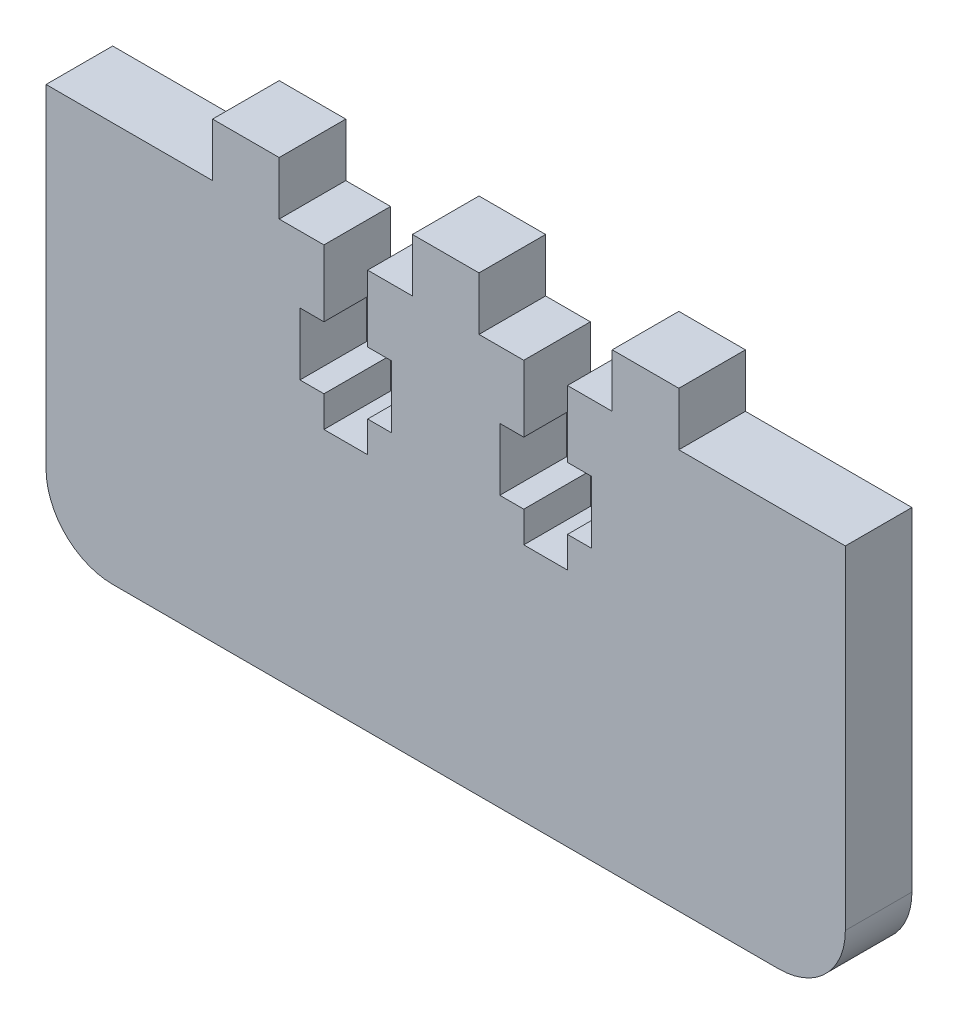
SolidWorks part; units mm, degrees
material "Acrylic (BLUE)"
ref_plane "Front Plane" through (0, 0, 0) normal (0, 0, 1) x (1, 0, 0)
ref_plane "Top Plane" through (0, 0, 0) normal (0, 1, 0) x (1, 0, 0)
ref_plane "Right Plane" through (0, 0, 0) normal (1, 0, 0) x (0, 0, -1)
sketch "Sketch1" plane through (0, 0, 0) normal (0, 0, 1) x (1, 0, 0)
  line L0 (-38.1, 19.05) -> (38.1, -19.05) construction
  line L1 (-38.1, 19.05) -> (38.1, 19.05)
  line L2 (-38.1, 19.05) -> (-38.1, -19.05)
  line L3 (-38.1, -19.05) -> (38.1, -19.05)
  line L4 (38.1, 19.05) -> (38.1, -19.05)
  dimension "D1" = 76.2
  dimension "D2" = 38.1
extrude "Boss-Extrude1" add sketch "Sketch1" along normal blind 6.35
sketch "Sketch2" plane through (0, 0, 6.35) normal (0, 0, 1) x (1, 0, 0)
  line L0 (0, 0) -> (0, 24.13) construction
  line L1 (38.1, 19.05) -> (-38.1, 19.05) construction
  line B0 (-11.6078, 19.05) -> (-11.6078, 12.7)
  line B1 (-11.6078, 12.7) -> (-13.8938, 12.7)
  line B2 (-13.8938, 12.7) -> (-13.8938, 6.7564)
  line B3 (-13.8938, 6.7564) -> (-11.6078, 6.7564)
  line B4 (-11.6078, 6.7564) -> (-11.6078, 3.81)
  line B5 (-11.6078, 3.81) -> (-7.4422, 3.81)
  line B6 (-7.4422, 3.81) -> (-7.4422, 6.7564)
  line B7 (-7.4422, 6.7564) -> (-5.1562, 6.7564)
  line B8 (-5.1562, 6.7564) -> (-5.1562, 12.7)
  line B9 (-5.1562, 12.7) -> (-7.4422, 12.7)
  line B10 (-7.4422, 12.7) -> (-7.4422, 19.05)
  line B11 (-7.4422, 19.05) -> (-3.175, 19.05)
  line B12 (-3.175, 19.05) -> (-3.175, 24.13)
  line B13 (-3.175, 24.13) -> (3.175, 24.13)
  line B14 (3.175, 24.13) -> (3.175, 19.05)
  line B15 (-11.6078, 19.05) -> (-15.875, 19.05)
  line B16 (-15.875, 19.05) -> (-15.875, 24.13)
  line B17 (-15.875, 24.13) -> (-22.225, 24.13)
  line B18 (-22.225, 24.13) -> (-22.225, 19.05)
  line B19 (-7.4422, 19.05) -> (-11.6078, 19.05) construction
  line B20 (22.225, 24.13) -> (22.225, 19.05)
  line B21 (7.4422, 19.05) -> (7.4422, 12.7)
  line B22 (7.4422, 12.7) -> (5.1562, 12.7)
  line B23 (5.1562, 12.7) -> (5.1562, 6.7564)
  line B24 (5.1562, 6.7564) -> (7.4422, 6.7564)
  line B25 (7.4422, 6.7564) -> (7.4422, 3.81)
  line B26 (7.4422, 3.81) -> (11.6078, 3.81)
  line B27 (11.6078, 3.81) -> (11.6078, 6.7564)
  line B28 (11.6078, 6.7564) -> (13.8938, 6.7564)
  line B29 (13.8938, 6.7564) -> (13.8938, 12.7)
  line B30 (13.8938, 12.7) -> (11.6078, 12.7)
  line B31 (11.6078, 12.7) -> (11.6078, 19.05)
  line B32 (15.875, 19.05) -> (15.875, 24.13)
  line B33 (15.875, 24.13) -> (22.225, 24.13)
  line B34 (7.4422, 19.05) -> (3.175, 19.05)
  line B35 (11.6078, 19.05) -> (7.4422, 19.05) construction
sketch_block_instance "NUT_HOLE_2X-1"
sketch_block "NUT_HOLE_2X" parameters "D1"=6.35, "D2"=4.1656, "D3"=25.4, "D4"=5.08, "D5"=8.7376, "D6"=5.9436, "D7"=6.35, "D8"=20.32, "D9"=2
sketch "Sketch3" plane through (0, 0, 6.35) normal (0, 0, 1) x (1, 0, 0)
  line L0 (22.225, 19.05) -> (15.875, 19.05)
  line L1 (-22.225, 24.13) -> (-22.225, 19.05) construction
  line L2 (-15.875, 24.13) -> (-22.225, 24.13) construction
  line L3 (-15.875, 19.05) -> (-15.875, 24.13) construction
  line L4 (-3.175, 24.13) -> (3.175, 24.13) construction
  line L5 (3.175, 24.13) -> (3.175, 19.05) construction
  line L6 (-3.175, 19.05) -> (-3.175, 24.13) construction
  line L7 (15.875, 24.13) -> (22.225, 24.13) construction
  line L8 (22.225, 24.13) -> (22.225, 19.05) construction
  line L9 (15.875, 19.05) -> (15.875, 24.13) construction
  line L10 (-22.225, 24.13) -> (-22.225, 19.05)
  line L11 (-15.875, 24.13) -> (-22.225, 24.13)
  line L12 (-15.875, 19.05) -> (-15.875, 24.13)
  line L13 (-3.175, 24.13) -> (3.175, 24.13)
  line L14 (3.175, 24.13) -> (3.175, 19.05)
  line L15 (-3.175, 19.05) -> (-3.175, 24.13)
  line L16 (15.875, 24.13) -> (22.225, 24.13)
  line L17 (22.225, 24.13) -> (22.225, 19.05)
  line L18 (15.875, 19.05) -> (15.875, 24.13)
  line L19 (-22.225, 19.05) -> (-15.875, 19.05)
  line L21 (-3.175, 19.05) -> (3.175, 19.05)
extrude "Boss-Extrude2" add sketch "Sketch3" against normal blind 6.35
sketch "Sketch6" plane through (0, 0, 6.35) normal (0, 0, 1) x (1, 0, 0)
  line L0 (-11.6078, 19.05) -> (-11.6078, 12.7) construction
  line L1 (-11.6078, 12.7) -> (-13.8938, 12.7) construction
  line L2 (-13.8938, 12.7) -> (-13.8938, 6.7564) construction
  line L3 (-13.8938, 6.7564) -> (-11.6078, 6.7564) construction
  line L4 (-11.6078, 6.7564) -> (-11.6078, 3.81) construction
  line L5 (-11.6078, 3.81) -> (-7.4422, 3.81) construction
  line L6 (-7.4422, 3.81) -> (-7.4422, 6.7564) construction
  line L7 (-7.4422, 6.7564) -> (-5.1562, 6.7564) construction
  line L8 (-5.1562, 6.7564) -> (-5.1562, 12.7) construction
  line L9 (-5.1562, 12.7) -> (-7.4422, 12.7) construction
  line L10 (-7.4422, 12.7) -> (-7.4422, 19.05) construction
  line L11 (7.4422, 19.05) -> (7.4422, 12.7) construction
  line L12 (7.4422, 12.7) -> (5.1562, 12.7) construction
  line L13 (5.1562, 12.7) -> (5.1562, 6.7564) construction
  line L14 (5.1562, 6.7564) -> (7.4422, 6.7564) construction
  line L15 (7.4422, 6.7564) -> (7.4422, 3.81) construction
  line L16 (11.6078, 3.81) -> (11.6078, 6.7564) construction
  line L17 (11.6078, 6.7564) -> (13.8938, 6.7564) construction
  line L18 (13.8938, 6.7564) -> (13.8938, 12.7) construction
  line L19 (13.8938, 12.7) -> (11.6078, 12.7) construction
  line L20 (11.6078, 12.7) -> (11.6078, 19.05) construction
  line L21 (7.4422, 3.81) -> (11.6078, 3.81) construction
  line L22 (-11.6078, 19.05) -> (-11.6078, 12.7)
  line L23 (-11.6078, 12.7) -> (-13.8938, 12.7)
  line L24 (-13.8938, 12.7) -> (-13.8938, 6.7564)
  line L25 (-13.8938, 6.7564) -> (-11.6078, 6.7564)
  line L26 (-11.6078, 6.7564) -> (-11.6078, 3.81)
  line L27 (-11.6078, 3.81) -> (-7.4422, 3.81)
  line L28 (-7.4422, 3.81) -> (-7.4422, 6.7564)
  line L29 (-7.4422, 6.7564) -> (-5.1562, 6.7564)
  line L30 (-5.1562, 6.7564) -> (-5.1562, 12.7)
  line L31 (-5.1562, 12.7) -> (-7.4422, 12.7)
  line L32 (-7.4422, 12.7) -> (-7.4422, 19.05)
  line L33 (7.4422, 19.05) -> (7.4422, 12.7)
  line L34 (7.4422, 12.7) -> (5.1562, 12.7)
  line L35 (5.1562, 12.7) -> (5.1562, 6.7564)
  line L36 (5.1562, 6.7564) -> (7.4422, 6.7564)
  line L37 (7.4422, 6.7564) -> (7.4422, 3.81)
  line L38 (11.6078, 3.81) -> (11.6078, 6.7564)
  line L39 (11.6078, 6.7564) -> (13.8938, 6.7564)
  line L40 (13.8938, 6.7564) -> (13.8938, 12.7)
  line L41 (13.8938, 12.7) -> (11.6078, 12.7)
  line L42 (11.6078, 12.7) -> (11.6078, 19.05)
  line L43 (7.4422, 3.81) -> (11.6078, 3.81)
  line L44 (-11.6078, 19.05) -> (-7.4422, 19.05)
  line L45 (7.4422, 19.05) -> (11.6078, 19.05)
extrude "Cut-Extrude1" cut sketch "Sketch6" against normal through all
fillet "Fillet1" radius 6.35 2 edges at (-38.1, -19.05, 3.175) (38.1, -19.05, 3.175)
